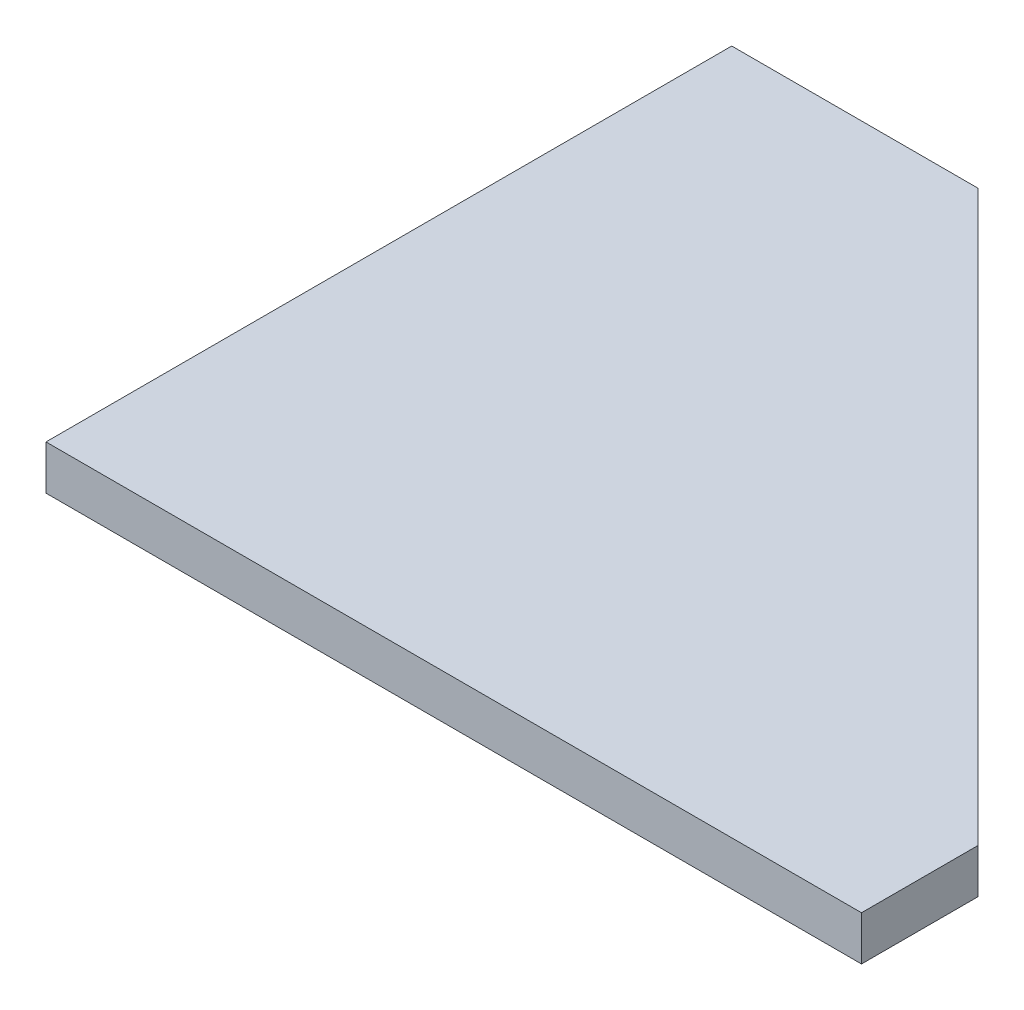
SolidWorks part; units mm, degrees
ref_plane "Front Plane" through (0, 0, 0) normal (0, 0, 1) x (1, 0, 0)
ref_plane "Top Plane" through (0, 0, 0) normal (0, 1, 0) x (1, 0, 0)
ref_plane "Right Plane" through (0, 0, 0) normal (1, 0, 0) x (0, 0, -1)
sketch "Sketch1" plane through (0, 0, 0) normal (0, 1, 0) x (1, 0, 0)
  line L0 (-138.61, 294.305) -> (350, -194.305)
  line L1 (-350, 294.305) -> (-138.61, 294.305)
  line L2 (-350, 294.305) -> (-350, -294.305)
  line L3 (-350, -294.305) -> (350, -294.305)
  line L4 (350, -194.305) -> (350, -294.305)
  line L5 (-350, 294.305) -> (350, -294.305) construction
  point P0 (0, 0)
  dimension "D1" = 588.61
  dimension "D2" = 700
  dimension "D3" = 100
  dimension "D4" = 45
extrude "Boss-Extrude1" add sketch "Sketch1" along normal blind 38.1
sketch "Sketch2" plane through (0, 0, 0) normal (0, -1, 0) x (1, 0, 0)
  line L5 (-350, -294.305) -> (-350, 294.305) construction
  line L6 (-350, -104.305) -> (-331, -104.305)
  line L7 (-350, -104.305) -> (-350, -154.305)
  line L8 (-350, -154.305) -> (-331, -154.305)
  line L9 (-331, -104.305) -> (-331, -154.305)
  line L10 (-138.61, -294.305) -> (-350, -294.305) construction
  line L11 (-350, 0) -> (155.695, 0) construction
  line L12 (350, 194.305) -> (-138.61, -294.305) construction
  line L13 (-331, 104.305) -> (-331, 154.305)
  line L14 (-350, 154.305) -> (-331, 154.305)
  line L15 (-350, 104.305) -> (-350, 154.305)
  line L16 (-350, 104.305) -> (-331, 104.305)
  dimension "D1" = 50
  dimension "D2" = 19
  dimension "D3" = 140
extrude "Cut-Extrude1" cut sketch "Sketch2" against normal blind 2
sketch "Sketch3" plane through (0, 0, 0) normal (0, 1, 0) x (1, 0, 0)
  line L0 (-138.61, 294.305) -> (-181.9465, 250.9685)
  line L1 (-181.9465, 250.9685) -> (-146.7069, 216.8915)
  line L2 (-146.7069, 216.8915) -> (-104.6689, 260.3639)
  line L3 (350, -194.305) -> (-138.61, 294.305) construction
  line L4 (-104.6689, 260.3639) -> (-138.61, 294.305)
  dimension "D1" = 48
extrude "Cut-Extrude2" cut sketch "Sketch3" along normal blind 20
